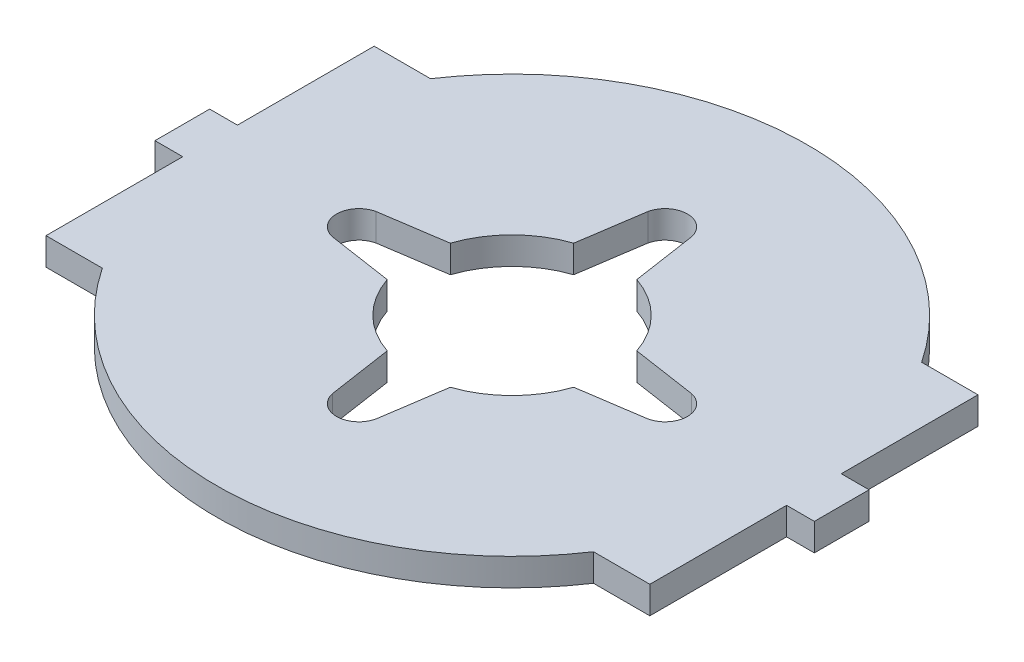
SolidWorks part; units mm, degrees
ref_plane "Front Plane" through (0, 0, 0) normal (0, 0, 1) x (1, 0, 0)
ref_plane "Top Plane" through (0, 0, 0) normal (0, 1, 0) x (1, 0, 0)
ref_plane "Right Plane" through (0, 0, 0) normal (1, 0, 0) x (0, 0, -1)
sketch "Sketch1" plane through (0, 0, 0) normal (0, 1, 0) x (1, 0, 0)
  line L1 (-35.052, -19.05) -> (35.052, -19.05)
  line L2 (-35.052, -19.05) -> (-35.052, 19.05)
  line L3 (-35.052, 19.05) -> (35.052, 19.05)
  line L4 (35.052, -19.05) -> (35.052, 19.05)
  line L5 (-35.052, -19.05) -> (35.052, 19.05) construction
  line L6 (-35.052, 19.05) -> (35.052, -19.05) construction
  point P0 (0, 0)
  dimension "D1" = 38.1
  dimension "D2" = 70.104
extrude "rectangular base" add sketch "Sketch1" along normal blind 3.175
sketch "Sketch2" plane through (0, 3.175, 0) normal (0, 1, 0) x (1, 0, 0)
  line L0 (0, 19.05) -> (0, 34.29) construction
  line L1 (35.052, 19.05) -> (-35.052, 19.05) construction
  line L2 (0, -19.05) -> (0, -35.56) construction
  line L3 (-35.052, -19.05) -> (35.052, -19.05) construction
  circle A2 centre (0, 0) radius 34.29
  dimension "D2" = 68.58
  dimension "D1" = 15.24
extrude "circular base add on" add sketch "Sketch2" against normal blind 3.175
sketch "Sketch3" plane through (0, 3.175, 0) normal (0, 1, 0) x (1, 0, 0)
  line L0 (0, 0) -> (0, 20.32) construction
  line L1 (0, 18.3061) -> (-2.54, 18.3061) construction
  line L2 (0, 18.3061) -> (2.54, 18.3061) construction
  line L3 (0, 5.588) -> (-4.445, 5.588) construction
  line L4 (0, 5.588) -> (4.445, 5.588) construction
  line L5 (-2.54, 18.3061) -> (-4.445, 5.588)
  line L6 (2.54, 18.3061) -> (4.445, 5.588)
  line L7 (-4.445, 5.588) -> (-5.8818, 4.1512)
  line L8 (4.445, 5.588) -> (5.8818, 4.1512)
  line L9 (-5.8818, 4.1512) -> (0, 0)
  line L10 (0, 0) -> (5.8818, 4.1512)
  arc A0 (-2.54, 18.3061) -> (2.54, 18.3061) centre (0, 17.7701) cw
  dimension "D1" = 20.32
  dimension "D2" = 2.54
  dimension "D3" = 2.54
  dimension "D4" = 4.445
  dimension "D5" = 5.588
  dimension "D6" = 135
  dimension "D7" = 2.032
  dimension "D8" = 135
  dimension "D9" = 2.032
extrude "hole for servo arm" cut sketch "Sketch3" against normal through all
sketch "Sketch4" plane through (0, 3.175, 0) normal (0, 1, 0) x (1, 0, 0)
  line L0 (-35.052, 0) -> (-35.052, 3.175)
  line L1 (-35.052, 19.05) -> (-35.052, -19.05) construction
  line L2 (-35.052, 3.175) -> (-38.2778, 3.175)
  line L3 (-38.2778, 3.175) -> (-38.2778, -3.175)
  line L4 (-38.2778, -3.175) -> (-35.052, -3.175)
  line L5 (-35.052, -3.175) -> (-35.052, 0)
  line L6 (0, 0) -> (-52.644, 0) construction
  dimension "D1" = 6.35
  dimension "D2" = 3.2258
extrude "tab" add sketch "Sketch4" against normal blind 3.175
mirror "Mirror1" about plane through (0, 0, 0) normal (1, 0, 0) of "tab"
pattern_circular "Circular pattern of servo arm hole" count 4 over 360 about axis through (0, 0, 0) along (0, 1, 0) of "hole for servo arm"
sketch "Sketch6" plane through (0, 3.175, 0) normal (0, 1, 0) x (1, 0, 0)
  circle A0 centre (0, 0) radius 11.43
  dimension "D1" = 22.86
extrude "Cut-Extrude2" cut sketch "Sketch6" against normal through all
